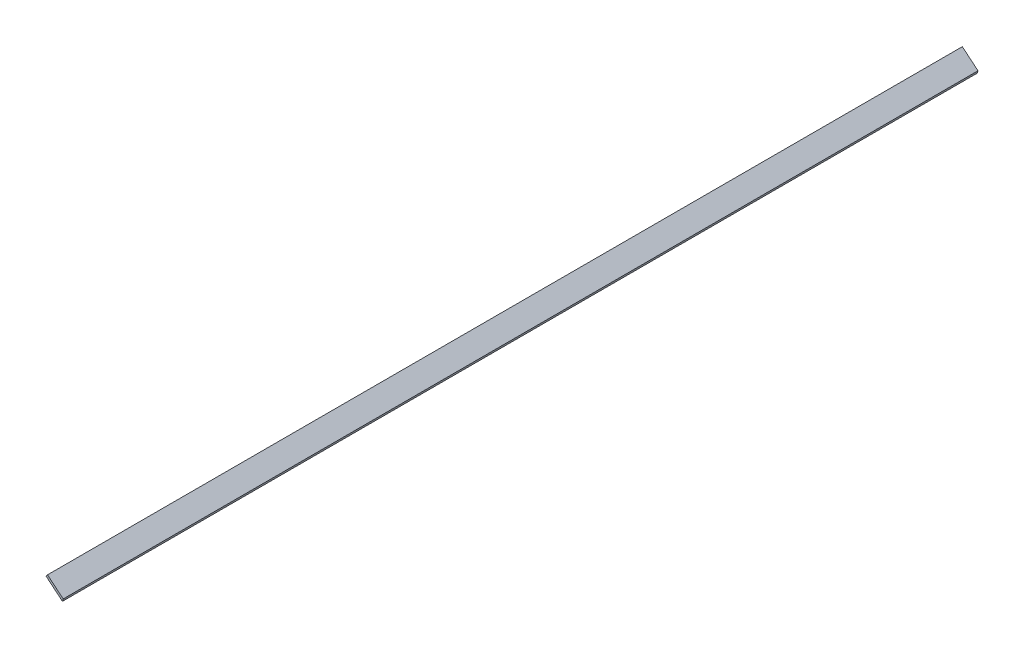
SolidWorks part; units mm, degrees
ref_plane "Front Plane" through (0, 0, 0) normal (0, 0, 1) x (1, 0, 0)
ref_plane "Top Plane" through (0, 0, 0) normal (0, 1, 0) x (1, 0, 0)
ref_plane "Right Plane" through (0, 0, 0) normal (1, 0, 0) x (0, 0, -1)
sketch "Sketch1" plane through (0, 0, 0) normal (0, 0, 1) x (1, 0, 0)
  line L0 (0, 0) -> (0.7605, 2.4411)
  line L1 (0.7605, 2.4411) -> (-14.6839, 15.3106)
  line L2 (-14.6839, 15.3106) -> (-16.196, 13.4959)
  line L3 (-16.196, 13.4959) -> (0, 0)
  dimension "D1" = 2.3622
  dimension "D2" = 90
  dimension "D3" = 67.5
  dimension "D4" = 21.082
extrude "Boss-Extrude1" add sketch "Sketch1" along normal blind 901.7
